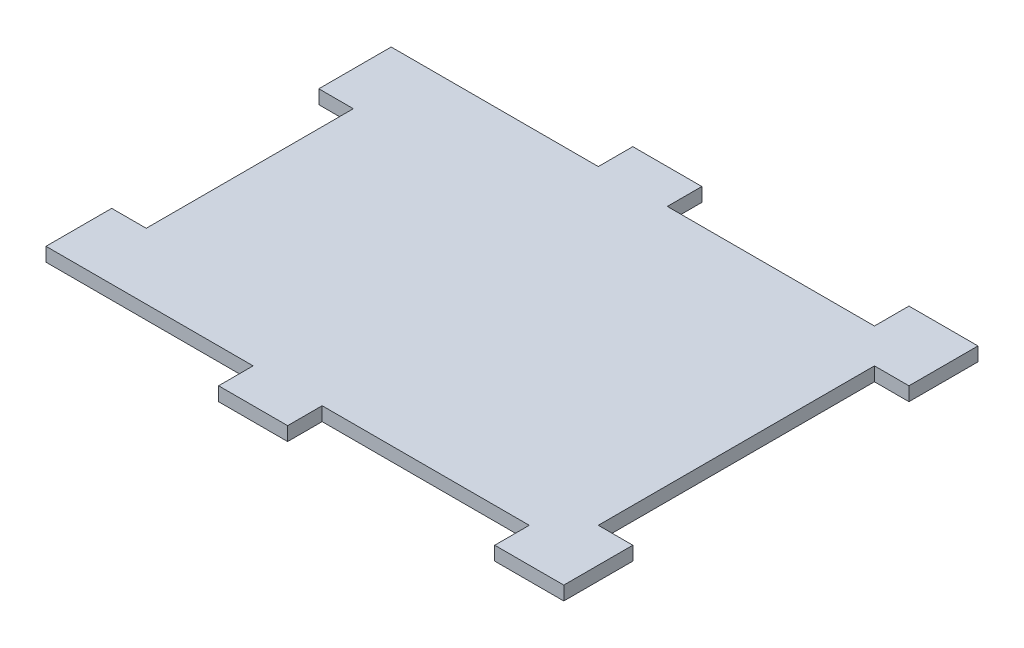
SolidWorks part; units mm, degrees
ref_plane "Front Plane" through (0, 0, 0) normal (0, 0, 1) x (1, 0, 0)
ref_plane "Top Plane" through (0, 0, 0) normal (0, 1, 0) x (1, 0, 0)
ref_plane "Right Plane" through (0, 0, 0) normal (1, 0, 0) x (0, 0, -1)
sketch "Sketch2" plane through (0, -382.6413, 0) normal (0, 1, 0) x (1, 0, 0)
  line L0 (78.6855, -59.9146) -> (72.3355, -59.9146)
  line L1 (78.6855, -47.2146) -> (65.9855, -47.2146)
  line L2 (78.6855, -47.2146) -> (78.6855, -59.9146)
  line L3 (78.6855, -123.4146) -> (65.9855, -123.4146)
  line L4 (-22.9145, -53.5646) -> (-22.9145, -66.8772)
  line L5 (72.3355, -59.9146) -> (72.3355, -110.7146)
  line L6 (72.3355, -110.7146) -> (78.6855, -110.7146)
  line L7 (78.6855, -110.7146) -> (78.6855, -123.4146)
  line L8 (65.9855, -123.4146) -> (65.9855, -117.0646)
  line L9 (65.9855, -117.0646) -> (27.8855, -117.0646)
  line L10 (27.8855, -117.0646) -> (27.8855, -123.4146)
  line L11 (27.8855, -123.4146) -> (15.1855, -123.4146)
  line L12 (15.1855, -123.4146) -> (15.1855, -117.0646)
  line L13 (15.1855, -117.0646) -> (-22.9145, -117.0646)
  line L14 (-22.9145, -117.0646) -> (-22.9145, -104.9772)
  line L15 (-22.9145, -104.9772) -> (-16.5645, -104.9772)
  line L16 (-16.5645, -104.9772) -> (-16.5645, -66.8772)
  line L17 (-16.5645, -66.8772) -> (-22.9145, -66.8772)
  line L18 (-22.9145, -66.8772) -> (-22.9145, -53.5646)
  line L19 (-22.9145, -53.5646) -> (15.1855, -53.5646)
  line L20 (15.1855, -53.5646) -> (15.1855, -47.2146)
  line L21 (15.1855, -47.2146) -> (27.8855, -47.2146)
  line L22 (27.8855, -47.2146) -> (27.8855, -53.5646)
  line L23 (27.8855, -53.5646) -> (65.9855, -53.5646)
  line L24 (65.9855, -53.5646) -> (65.9855, -47.2146)
  line L25 (65.9855, -47.2146) -> (78.6855, -47.2146)
  line L41 (78.6855, -110.7146) -> (78.6855, -123.4146)
  line L42 (27.8855, -47.2146) -> (15.1855, -47.2146)
  line L43 (-22.9145, -104.9772) -> (-22.9145, -123.4146)
  line L44 (27.8855, -123.4146) -> (15.1855, -123.4146)
  circle M16 centre (27.8855, -120.8746) radius 1.5875
  circle M17 centre (27.8855, -49.7546) radius 1.5875
  circle M18 centre (76.1455, -49.7546) radius 1.5875
  circle M19 centre (76.1455, -120.8746) radius 1.5875
  line M23 (65.9855, -117.3186) -> (65.9855, -123.4146)
  line M24 (65.9855, -123.4146) -> (78.6855, -123.4146)
  line M25 (78.6855, -123.4146) -> (78.6855, -47.2146)
  line M26 (78.6855, -47.2146) -> (65.9855, -47.2146)
  line M27 (65.9855, -47.2146) -> (65.9855, -53.3106)
  line M30 (40.5855, -47.2146) -> (15.1855, -47.2146)
  line M31 (15.1855, -47.2146) -> (15.1855, -53.3106)
  line M35 (-22.9145, -47.2146) -> (-22.9145, -72.6146)
  line M39 (-22.9145, -98.0146) -> (-22.9145, -123.4146)
  line M43 (15.1855, -117.3186) -> (15.1855, -123.4146)
  line M44 (15.1855, -123.4146) -> (40.5855, -123.4146)
extrude "Boss-Extrude1" add sketch "Sketch2" along normal blind 2.54 contours L10 M16 | M19 | M18 | L22 M17 | L24 L23 L22 L20 L19 L17 L16 L15 L13 L12 L10 L9 L8 L6 L5 L0 M17 M30 M31 M35 M39 M43 M44 M16 M23 M24 M25 M26 M27 M19 M18
